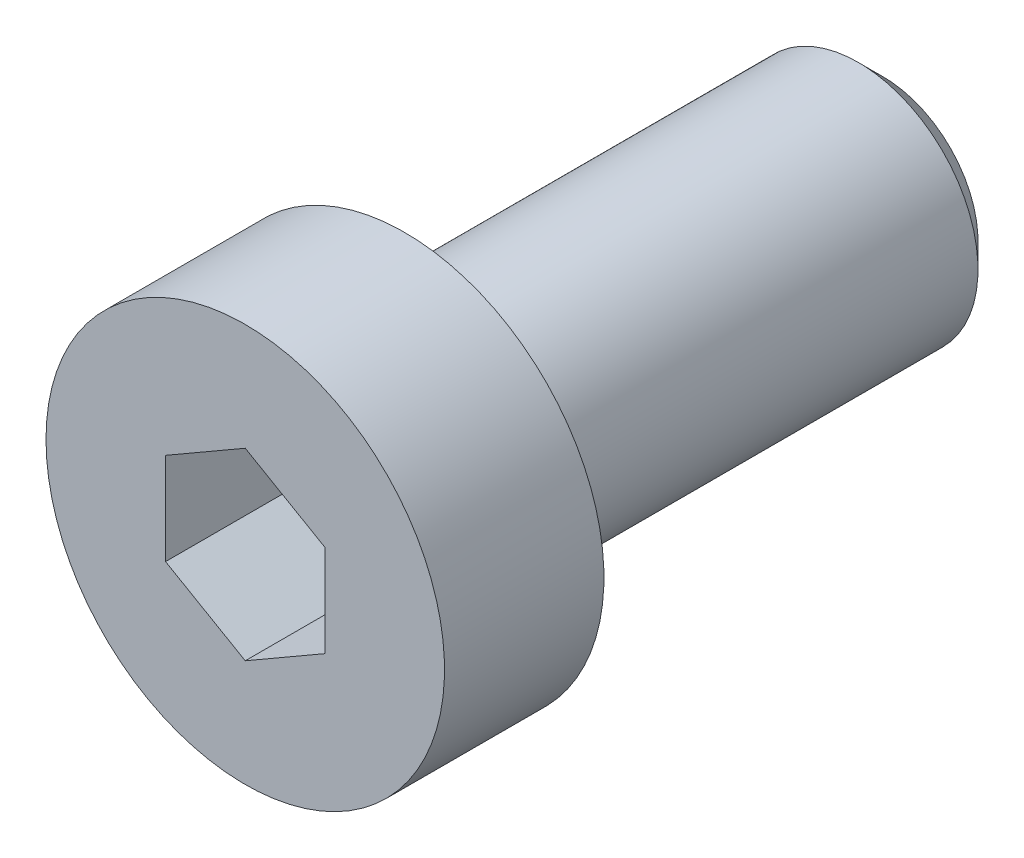
SolidWorks part; units mm, degrees
ref_plane "Piano frontale" through (0, 0, 0) normal (0, 0, 1) x (1, 0, 0)
ref_plane "Piano superiore" through (0, 0, 0) normal (0, 1, 0) x (1, 0, 0)
ref_plane "Piano destro" through (0, 0, 0) normal (1, 0, 0) x (0, 0, -1)
ref_plane "Plane1" through (0, 21.5, 0) normal (0, -1, 0) x (1, 0, 0)
sketch "Sketch1" plane through (0, 21.5, 0) normal (0, -1, 0) x (1, 0, 0)
  line L0 (-10.5, -0.4) -> (-15.5, -0.4)
  line L1 (-15.5, -0.4) -> (-15.5, -4.4)
  line L2 (-15.5, -4.4) -> (-10.5, -4.4)
  line L3 (-10.5, -4.4) -> (-10.5, -0.4)
  line L4 (-15.5, -0.4) -> (-15.5, -4.4) construction
revolve "Revolve1" add sketch "Sketch1" angle 360 about L4
sketch "Sketch2" plane through (0, 0, -4.4) normal (0, 0, -1) x (-1, 0, 0)
  circle A0 centre (15.5, 21.5) radius 3
extrude "Extrude1" add sketch "Sketch2" along normal blind 12
sketch "Sketch3" plane through (0, 0, -0.4) normal (0, 0, 1) x (1, 0, 0)
  line L0 (-17.5, 22.6547) -> (-17.5, 20.3453)
  line L1 (-17.5, 20.3453) -> (-15.5, 19.1906)
  line L2 (-15.5, 19.1906) -> (-13.5, 20.3453)
  line L3 (-13.5, 20.3453) -> (-13.5, 22.6547)
  line L4 (-13.5, 22.6547) -> (-15.5, 23.8094)
  line L5 (-15.5, 23.8094) -> (-17.5, 22.6547)
extrude "Extrude2" cut sketch "Sketch3" against normal blind 3
sketch "Sketch4" plane through (0, 21.5, 0) normal (0, -1, 0) x (1, 0, 0)
  line L0 (-13.5, -3.4) -> (-15.5, -3.4)
  line L1 (-15.5, -3.4) -> (-15.5, -4.1279)
  line L2 (-15.5, -4.1279) -> (-13.5, -3.4)
  line L3 (-15.5, -3.4) -> (-15.5, -4.128) construction
revolve "Cut-Revolve1" cut sketch "Sketch4" angle 360 about L3
chamfer "Chamfer1" distance 0.6135 angle 45 1 edges at (-18.5, 21.5, -16.4)
fillet "Fillet1" radius 0.2 1 edges at (-18.5, 21.5, -4.4)
